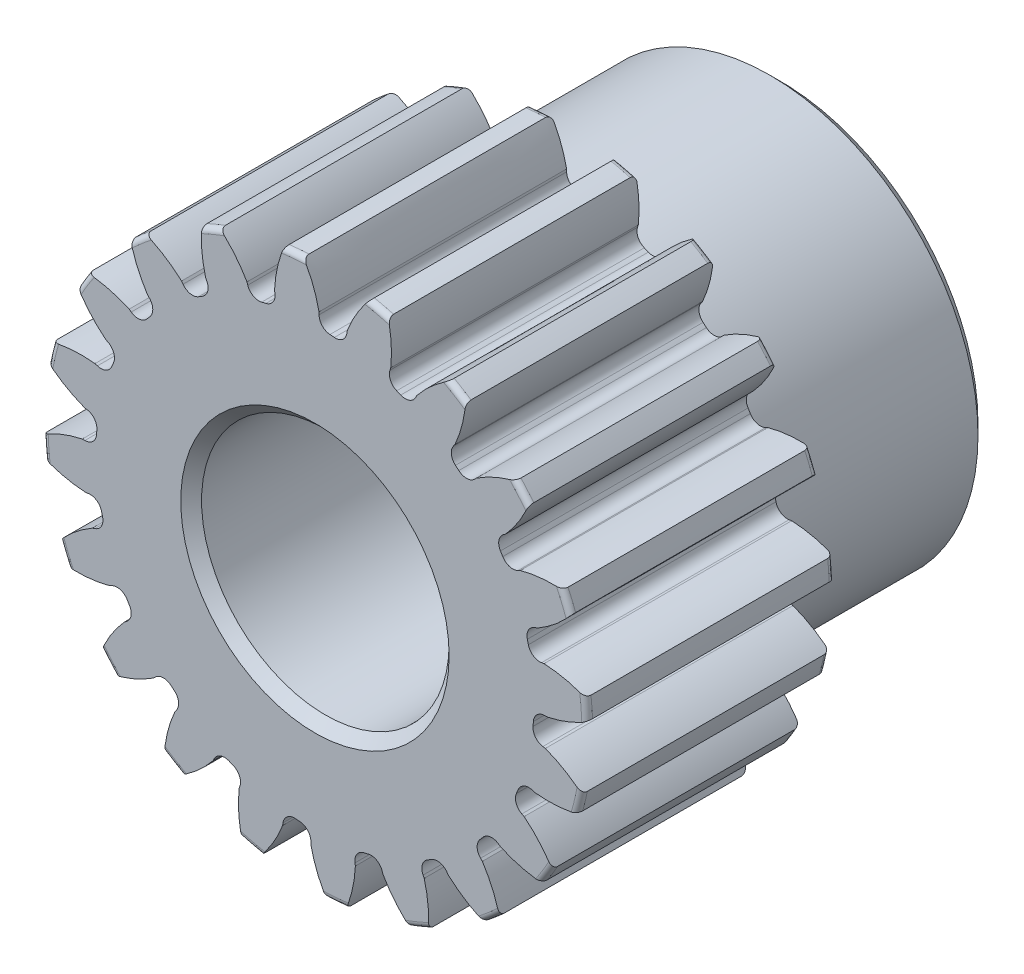
SolidWorks part; units mm, degrees
ref_plane "Front" through (0, 0, 0) normal (0, 0, 1) x (1, 0, 0)
ref_plane "Top" through (0, 0, 0) normal (0, 1, 0) x (1, 0, 0)
ref_plane "Right" through (0, 0, 0) normal (1, 0, 0) x (0, 0, -1)
sketch "Sketch1" plane through (0, 0, 0) normal (0, 0, 1) x (1, 0, 0)
  line L0 (-254, 0) -> (254, 0) construction
  circle A0 centre (0, 0) radius 13.97
  circle A1 centre (0, 0) radius 12.7 construction
  circle A3 centre (0, 0) radius 11.2306 construction
  dimension "D1" = 1.4694
  dimension "OD" = 27.94
  dimension "Ptich Dia" = 25.4
  dimension "D2" = 2.7394
  dimension "Root Dia" = 22.4612
  dimension "D3" = 1.27
  dimension "Number of Teeth" = 508
extrude "Boss-Extrude1" add sketch "Sketch1" against normal blind 12.7
sketch "Sketch2" plane through (0, 0, 0) normal (1, 0, 0) x (0, 0, -1)
  line L0 (12.7, 0) -> (23.876, 0)
  line L1 (12.7, 0) -> (12.7, 10.668)
  line L2 (12.7, 10.668) -> (23.876, 10.668)
  line L3 (23.876, 10.668) -> (23.876, 0)
  point P5 (23.876, -10.668)
  point P6 (0, -13.97)
  point P7 (12.7, -13.97)
  point P9 (0, 13.97)
  dimension "Face Wd" = 12.7
  dimension "B Hub Dia" = 21.336
  dimension "D O'all Lg." = 23.876
revolve "Revolve1" add sketch "Sketch2" angle 360 about L0
fillet "Fillet2" radius 0.2794 3 edges at (13.97, 0, -12.7) (13.97, 0, 0) (10.668, 0, -12.7)
sketch "Sketch3" plane through (0, 0, 0) normal (0, 0, 1) x (1, 0, 0)
  line L0 (0, 0) -> (0, 13.97) construction
  line L1 (-4.0817, 11.2144) -> (0, 12.7)
  line L2 (-9.5921, 12.7) -> (9.5921, 12.7) construction
  line L3 (-9.0136, 9.4193) -> (9.0136, 15.9807) construction
  line L4 (-4.0817, 11.2144) -> (0, 0) construction
  line L5 (-9.951, 6.5878) -> (0, 0) construction
  line L6 (-9.951, 6.5878) -> (-3.3571, 16.548) construction
  line L7 (-2.8353, 11.5924) -> (0, 0) construction
  line L8 (-2.8353, 11.5924) -> (0.1182, 12.3148) construction
  arc A0 (-4.0817, 11.2144) -> (-9.951, 6.5878) centre (0, 0) ccw
  circle A1 centre (0, 0) radius 12.7 construction
  circle A2 centre (0, 0) radius 11.9341 construction
  arc A3 (-4.0817, 11.2144) -> (-2.8353, 11.5924) centre (0, 0) cw
  circle A4 centre (0, 0) radius 13.97 construction
  point P6 (0, 12.7)
  dimension "D1" = 4.3437
  dimension "Pressure Angle" = 20
  dimension "D2" = 7.6014
  dimension "D3" = 11.9451
  dimension "D4" = 1.3031
  dimension "D5" = 3.0406
sketch "Sketch4" plane through (0, 0, 0) normal (0, 0, 1) x (1, 0, 0)
  line L0 (0, 0) -> (0.9934, 12.6218) construction
  line L1 (0.2108, 11.9322) -> (0.2108, 11.2286)
  line L2 (0, 12.7) -> (1.9867, 12.5436) construction
  line L3 (1.6584, 11.8183) -> (1.5483, 11.1234)
  line L4 (0.2108, 11.2286) -> (0, 0) construction
  line L5 (0, 0) -> (0, 13.97) construction
  line L6 (-9.951, 6.5878) -> (-3.3571, 16.548) construction
  line L7 (-9.951, 6.5878) -> (-3.3571, 16.548) construction
  arc A0 (1.5483, 11.1234) -> (0.2108, 11.2286) centre (0, 0) ccw
  arc A1 (0, 12.7) -> (1.9867, 12.5436) centre (0, 0) cw construction
  circle A2 centre (0, 0) radius 12.7 construction
  circle A3 centre (0, 0) radius 11.9341 construction
  circle A4 centre (0, 0) radius 11.2306 construction
  arc A5 (5.9045, 15.8191) -> (-3.3571, 16.548) centre (0, 0) ccw
  spline S0 degree 2 poles (-3.3571, 16.548) (-0.4015, 14.8243) (0.2108, 11.9322) knots 0 0 0 1 1 1
  spline S1 degree 2 poles (5.9045, 15.8191) (2.7156, 14.579) (1.6584, 11.8183) knots 0 0 0 1 1 1
  dimension "D1" = 1.9949
extrude "Cut-Extrude1" cut sketch "Sketch4" against normal through all
fillet "Fillet1" radius 0.5985 2 edges at (1.5483, 11.1234, -6.35) (0.2108, 11.2286, -6.35)
pattern_circular "CirPattern1" count 20 over 360 about axis through (0, 0, -12.7) along (0, 0, 1) of "Cut-Extrude1", "Fillet1"
sketch "Sketch5" plane through (0, 0, 0) normal (0, 0, 1) x (1, 0, 0)
  circle A0 centre (0, 0) radius 6.35
  circle A1 centre (0, 0) radius 6.35 construction
  dimension "Bore Min" = 12.7
  dimension "Bore Max" = 12.7
extrude "Cut-Extrude2" cut sketch "Sketch5" against normal through all
chamfer "Chamfer1" distance 0.5334 angle 45 3 edges at (10.668, 0, -23.876) (6.35, 0, 0) (6.35, 0, -23.876)
sketch "Pitch Dia" plane through (0, 0, 0) normal (0, 0, 1) x (1, 0, 0)
  circle A0 centre (0, 0) radius 12.7 construction
  circle A1 centre (0, 0) radius 12.7 construction
equation "\"D1@Boss-Extrude1\" = \"Face Wd@Sketch2\""
equation "\"D2@Sketch3\" = \"D1@Sketch3\"*1.75"
equation "\"D3@Sketch3\" = \"D1@Sketch3\"+\"D2@Sketch3\""
equation "\"D4@Sketch3\" = \"D1@Sketch3\"*.3"
equation "\"D5@Sketch3\" = \"D1@Sketch3\"-\"D4@Sketch3\""
equation "\"D1@Sketch4\" = 1.5708/(\"Number of Teeth@Sketch1\"/\"Ptich Dia@Sketch1\")"
equation "\"D1@Chamfer1\" = \"B Hub Dia@Sketch2\"*.025"
equation "\"D1@CirPattern1\" = \"Number of Teeth@Sketch1\""
equation "\"D1@Fillet1\" = \"D1@Sketch4\"*.3"
equation "\"D1@Fillet2\" = \"OD@Sketch1\"*.01"
equation "\"D1@Sketch1\" = 1.157/(\"Number of Teeth@Sketch1\"/\"Ptich Dia@Sketch1\")"
